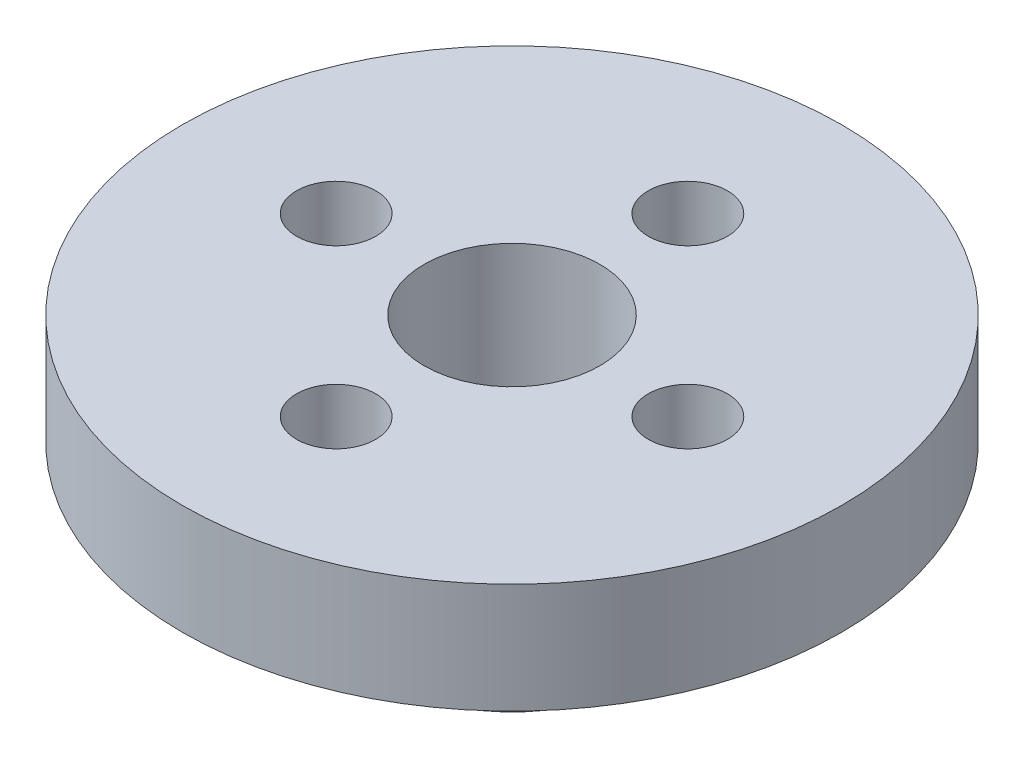
SolidWorks part; units mm, degrees
ref_plane "Front Plane" through (0, 0, 0) normal (0, 0, 1) x (1, 0, 0)
ref_plane "Top Plane" through (0, 0, 0) normal (0, 1, 0) x (1, 0, 0)
ref_plane "Right Plane" through (0, 0, 0) normal (1, 0, 0) x (0, 0, -1)
sketch "Sketch1" plane through (0, 0, 0) normal (0, 1, 0) x (1, 0, 0)
  circle A0 centre (0, 0) radius 9.525
  dimension "D1" = 19.05
extrude "Boss-Extrude1" add sketch "Sketch1" along normal blind 3.175
sketch "Sketch2" plane through (0, 0, 0) normal (0, 1, 0) x (1, 0, 0)
  circle A0 centre (0, 0) radius 3.81
  circle A1 centre (0, 0) radius 2.54
  dimension "D1" = 5.08
  dimension "D2" = 7.62
extrude "Boss-Extrude2" add sketch "Sketch2" against normal blind 4.064
sketch "Sketch3" plane through (0, 0, 0) normal (0, 1, 0) x (1, 0, 0)
  circle A0 centre (0, 0) radius 2.54
  circle A1 centre (5.08, 0) radius 1.143
  circle A2 centre (0, 5.08) radius 1.143
  circle A3 centre (-5.08, 0) radius 1.143
  circle A4 centre (0, -5.08) radius 1.143
  point P11 (0, 0)
  point P12 (0, 0)
  point P13 (0, 0)
  point P14 (0, 0)
  dimension "D1" = 5.08
  dimension "D3" = 2.286
  dimension "D4" = 2.286
  dimension "D6" = 2.286
  dimension "D9" = 2.286
  dimension "D2" = 5.08
  dimension "D5" = 5.08
  dimension "D7" = 5.08
  dimension "D8" = 5.08
extrude "Cut-Extrude1" cut sketch "Sketch3" along normal blind 3.175
